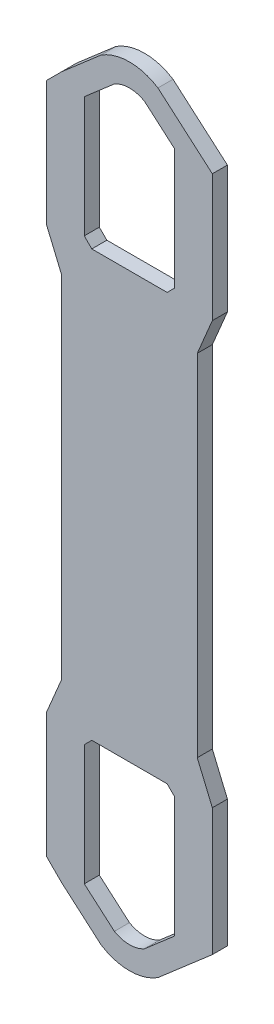
SolidWorks part; units mm, degrees
material "Acrylic (Medium-high impact)"
ref_plane "Front Plane" through (0, 0, 0) normal (0, 0, 1) x (1, 0, 0)
ref_plane "Top Plane" through (0, 0, 0) normal (0, 1, 0) x (1, 0, 0)
ref_plane "Right Plane" through (0, 0, 0) normal (1, 0, 0) x (0, 0, -1)
sketch "Sketch1" plane through (0, 0, 0) normal (0, 0, 1) x (1, 0, 0)
  line L0 (0, 0) -> (0, -8.6603) construction
  line L1 (-25, 0) -> (-5, -17.3205) construction
  line L2 (25, 0) -> (5, -17.3205) construction
  line L3 (15, -8.6603) -> (-15, -8.6603) construction
  line L4 (15, -8.6603) -> (15, 31.3397)
  line L5 (-15, -8.6603) -> (-15, 31.3397)
  line L6 (15, -8.6603) -> (5, -17.3205)
  line L7 (-5, -17.3205) -> (-15, -8.6603)
  line L8 (-15, 31.3397) -> (-12.5, 33.8397)
  line L9 (15, 31.3397) -> (12.5, 33.8397)
  line L10 (12.5, 33.8397) -> (-12.5, 33.8397)
  line L11 (15.6066, 41.3397) -> (-15.6066, 41.3397)
  line L12 (-22.5, 34.4463) -> (-15.6066, 41.3397)
  line L13 (-22.5, -12.0866) -> (-22.5, 34.4463)
  line L14 (-15, 31.3397) -> (15, 31.3397) construction
  line L15 (-9.445, -23.3926) -> (-22.5, -12.0866)
  line L16 (22.5, -12.0866) -> (9.445, -23.3926)
  line L17 (22.5, -12.0866) -> (22.5, 34.4463)
  line L18 (22.5, 34.4463) -> (15.6066, 41.3397)
  line L19 (-22.5, 34.4463) -> (-22.5, 174.4463)
  line L20 (-22.5, 104.4463) -> (22.5, 104.4463) construction
  line L21 (22.5, 174.4463) -> (22.5, 34.4463)
  line L22 (-15, 177.5529) -> (15, 177.5529) construction
  line L23 (15, 217.5529) -> (-15, 217.5529) construction
  line L24 (25, 208.8927) -> (5, 226.2132) construction
  line L25 (-25, 208.8927) -> (-5, 226.2132) construction
  line L26 (0, 208.8927) -> (0, 217.5529) construction
  line L27 (22.5, 174.4463) -> (15.6066, 167.5529)
  line L28 (22.5, 220.9793) -> (22.5, 174.4463)
  line L29 (22.5, 220.9793) -> (9.445, 232.2853)
  line L30 (-9.445, 232.2853) -> (-22.5, 220.9793)
  line L31 (-22.5, 220.9793) -> (-22.5, 174.4463)
  line L32 (-22.5, 174.4463) -> (-15.6066, 167.5529)
  line L33 (15.6066, 167.5529) -> (-15.6066, 167.5529)
  line L34 (12.5, 175.0529) -> (-12.5, 175.0529)
  line L35 (15, 177.5529) -> (12.5, 175.0529)
  line L36 (-15, 177.5529) -> (-12.5, 175.0529)
  line L37 (-5, 226.2132) -> (-15, 217.5529)
  line L38 (15, 217.5529) -> (5, 226.2132)
  line L39 (-15, 217.5529) -> (-15, 177.5529)
  line L40 (15, 217.5529) -> (15, 177.5529)
  line L41 (27.5, -14.3709) -> (27.5, 34.4463) construction
  line L42 (27.5, -14.3709) -> (12.4635, -27.3929) construction
  line L43 (-12.4635, -27.3929) -> (-27.5, -14.3709) construction
  line L44 (-27.5, -14.3709) -> (-27.5, 34.4463) construction
  line L45 (-27.5, 29.4463) -> (-27.5, 34.4463)
  line L46 (-22.5, -12.0866) -> (-27.5, -7.0866)
  line L47 (-27.5, 29.4463) -> (-27.5, -7.0866)
  line L48 (22.5, 34.4463) -> (27.5, 29.4463)
  line L49 (22.5, -12.0866) -> (27.5, -7.7565)
  line L50 (27.5, -7.7565) -> (27.5, 29.4463)
  line L51 (-22.5, 46.3397) -> (22.5, 46.3397) construction
  line L52 (-27.5, 34.4463) -> (-22.5, 46.3397)
  line L53 (27.5, 34.4463) -> (22.5, 46.3397)
  line L54 (27.5, 34.4463) -> (27.5, 29.4463)
  line L55 (-27.5, 29.4463) -> (-22.5, 34.4463) construction
  line L56 (22.5, 220.9793) -> (27.5, 216.6492)
  line L57 (27.5, 216.6492) -> (27.5, 179.4463)
  line L58 (27.5, 174.4463) -> (27.5, 179.4463)
  line L59 (27.5, 174.4463) -> (22.5, 162.5529)
  line L60 (-22.5, 220.9793) -> (-27.5, 215.9793)
  line L61 (-27.5, 179.4463) -> (-27.5, 174.4463)
  line L62 (-27.5, 179.4463) -> (-27.5, 215.9793)
  line L63 (-27.5, 174.4463) -> (-22.5, 162.5529)
  arc A0 (9.445, -23.3926) -> (-9.445, -23.3926) centre (0, -8.6603) cw
  circle A1 centre (0, -8.6603) radius 10 construction
  circle A2 centre (0, 217.5529) radius 10 construction
  arc A3 (5, -17.3205) -> (-5, -17.3205) centre (0, -8.6603) cw
  arc A4 (5, 226.2132) -> (-5, 226.2132) centre (0, 217.5529) ccw
  arc A5 (9.445, 232.2853) -> (-9.445, 232.2853) centre (0, 217.5529) ccw
  arc A6 (12.4635, -27.3929) -> (-12.4635, -27.3929) centre (0, -8.6603) cw construction
  dimension "D1" = 10
  dimension "D3" = 20
  dimension "D4" = 40
  dimension "D5" = 45
  dimension "D8" = 7.5
  dimension "D2" = 30
  dimension "D7" = 2.5
  dimension "D6" = 45
  dimension "D9" = 70
  dimension "D11" = 5
  dimension "D10" = 5
extrude "Boss-Extrude1" add sketch "Sketch1" along normal blind 5 contours A0 L16 L17 L18 L11 L12 L13 L15 L6 A3 L7 L5 L8 L10 L9 L4 | L27 L33 L32 L19 L12 L11 L18 L21 | L29 A5 L30 L31 L32 L33 L27 L28 A4 L38 L40 L35 L34 L36 L39 L37 | L52 L45 L47 L46 L13 L19 | L49 L50 L48 L17 | L54 L53 L21 L48 | L59 L58 L57 L56 L28 L21 | L61 L63 L19 L31 L60 L62
